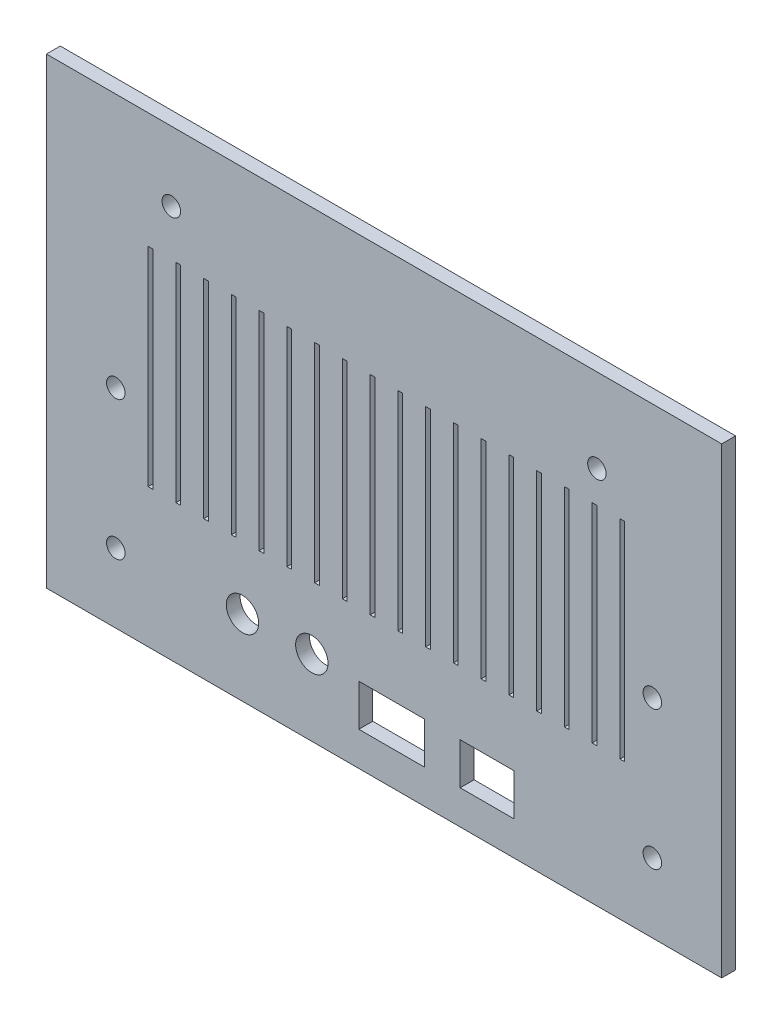
SolidWorks part; units mm, degrees
ref_plane "Front Plane" through (0, 0, 0) normal (0, 0, 1) x (1, 0, 0)
ref_plane "Top Plane" through (0, 0, 0) normal (0, 1, 0) x (1, 0, 0)
ref_plane "Right Plane" through (0, 0, 0) normal (1, 0, 0) x (0, 0, -1)
sketch "Sketch1" plane through (0, 0, 0) normal (0, 0, 1) x (1, 0, 0)
  line L1 (-48.2442, 79.6334) -> (97.7558, 79.6334)
  line L2 (-48.2442, 79.6334) -> (-48.2442, -20.3666)
  line L3 (-48.2442, -20.3666) -> (97.7558, -20.3666)
  line L4 (97.7558, 79.6334) -> (97.7558, -20.3666)
  dimension "D1" = 146
  dimension "D2" = 100
extrude "Boss-Extrude1" add sketch "Sketch1" along normal blind 3
sketch "Sketch2" plane through (0, 0, 3) normal (0, 0, 1) x (1, 0, 0)
  line L0 (-20.2442, 54.6334) -> (-19.2442, 54.6334)
  line L1 (-26.2442, 54.6334) -> (-25.2442, 54.6334)
  line L2 (-26.2442, 54.6334) -> (-26.2442, 9.6334)
  line L3 (-26.2442, 9.6334) -> (-25.2442, 9.6334)
  line L4 (-25.2442, 54.6334) -> (-25.2442, 9.6334)
  line L5 (-20.2442, 54.6334) -> (-20.2442, 9.6334)
  line L6 (-20.2442, 9.6334) -> (-19.2442, 9.6334)
  line L7 (-19.2442, 54.6334) -> (-19.2442, 9.6334)
  line L8 (-14.2442, 54.6334) -> (-13.2442, 54.6334)
  line L9 (-14.2442, 54.6334) -> (-14.2442, 9.6334)
  line L10 (-14.2442, 9.6334) -> (-13.2442, 9.6334)
  line L11 (-13.2442, 54.6334) -> (-13.2442, 9.6334)
  line L12 (-8.2442, 54.6334) -> (-7.2442, 54.6334)
  line L13 (-8.2442, 54.6334) -> (-8.2442, 9.6334)
  line L14 (-8.2442, 9.6334) -> (-7.2442, 9.6334)
  line L15 (-7.2442, 54.6334) -> (-7.2442, 9.6334)
  line L16 (-2.2442, 54.6334) -> (-1.2442, 54.6334)
  line L17 (-2.2442, 54.6334) -> (-2.2442, 9.6334)
  line L18 (-2.2442, 9.6334) -> (-1.2442, 9.6334)
  line L19 (-1.2442, 54.6334) -> (-1.2442, 9.6334)
  line L20 (3.7558, 54.6334) -> (4.7558, 54.6334)
  line L21 (3.7558, 54.6334) -> (3.7558, 9.6334)
  line L22 (3.7558, 9.6334) -> (4.7558, 9.6334)
  line L23 (4.7558, 54.6334) -> (4.7558, 9.6334)
  line L24 (-48.2442, 79.6334) -> (-48.2442, -20.3666) construction
  line L25 (-48.2442, -20.3666) -> (97.7558, -20.3666) construction
  line L26 (9.7558, 54.6334) -> (10.7558, 54.6334)
  line L27 (9.7558, 54.6334) -> (9.7558, 9.6334)
  line L28 (9.7558, 9.6334) -> (10.7558, 9.6334)
  line L29 (10.7558, 54.6334) -> (10.7558, 9.6334)
  line L30 (15.7558, 54.6334) -> (16.7558, 54.6334)
  line L31 (15.7558, 54.6334) -> (15.7558, 9.6334)
  line L32 (15.7558, 9.6334) -> (16.7558, 9.6334)
  line L33 (16.7558, 54.6334) -> (16.7558, 9.6334)
  line L34 (21.7558, 54.6334) -> (22.7558, 54.6334)
  line L35 (21.7558, 54.6334) -> (21.7558, 9.6334)
  line L36 (21.7558, 9.6334) -> (22.7558, 9.6334)
  line L37 (22.7558, 54.6334) -> (22.7558, 9.6334)
  line L38 (33.7558, 54.6334) -> (34.7558, 54.6334)
  line L39 (27.7558, 54.6334) -> (28.7558, 54.6334)
  line L40 (27.7558, 54.6334) -> (27.7558, 9.6334)
  line L41 (27.7558, 9.6334) -> (28.7558, 9.6334)
  line L42 (28.7558, 54.6334) -> (28.7558, 9.6334)
  line L43 (33.7558, 54.6334) -> (33.7558, 9.6334)
  line L44 (33.7558, 9.6334) -> (34.7558, 9.6334)
  line L45 (34.7558, 54.6334) -> (34.7558, 9.6334)
  line L46 (39.7558, 54.6334) -> (40.7558, 54.6334)
  line L47 (39.7558, 54.6334) -> (39.7558, 9.6334)
  line L48 (39.7558, 9.6334) -> (40.7558, 9.6334)
  line L49 (40.7558, 54.6334) -> (40.7558, 9.6334)
  line L50 (45.7558, 54.6334) -> (46.7558, 54.6334)
  line L51 (45.7558, 54.6334) -> (45.7558, 9.6334)
  line L52 (45.7558, 9.6334) -> (46.7558, 9.6334)
  line L53 (46.7558, 54.6334) -> (46.7558, 9.6334)
  line L54 (51.7558, 54.6334) -> (52.7558, 54.6334)
  line L55 (51.7558, 54.6334) -> (51.7558, 9.6334)
  line L56 (51.7558, 9.6334) -> (52.7558, 9.6334)
  line L57 (52.7558, 54.6334) -> (52.7558, 9.6334)
  line L58 (57.7558, 54.6334) -> (58.7558, 54.6334)
  line L59 (57.7558, 54.6334) -> (57.7558, 9.6334)
  line L60 (57.7558, 9.6334) -> (58.7558, 9.6334)
  line L61 (58.7558, 54.6334) -> (58.7558, 9.6334)
  line L62 (63.7558, 54.6334) -> (64.7558, 54.6334)
  line L63 (63.7558, 54.6334) -> (63.7558, 9.6334)
  line L64 (63.7558, 9.6334) -> (64.7558, 9.6334)
  line L65 (64.7558, 54.6334) -> (64.7558, 9.6334)
  line L66 (69.7558, 54.6334) -> (70.7558, 54.6334)
  line L67 (69.7558, 54.6334) -> (69.7558, 9.6334)
  line L68 (69.7558, 9.6334) -> (70.7558, 9.6334)
  line L69 (70.7558, 54.6334) -> (70.7558, 9.6334)
  line L70 (75.7558, 54.6334) -> (76.7558, 54.6334)
  line L71 (75.7558, 54.6334) -> (75.7558, 9.6334)
  line L72 (75.7558, 9.6334) -> (76.7558, 9.6334)
  line L73 (76.7558, 54.6334) -> (76.7558, 9.6334)
  line L74 (97.7558, -20.3666) -> (97.7558, 79.6334) construction
  dimension "D1" = 1
  dimension "D2" = 45
  dimension "D3" = 45
  dimension "D4" = 45
  dimension "D5" = 45
  dimension "D6" = 45
  dimension "D7" = 5
  dimension "D8" = 5
  dimension "D9" = 5
  dimension "D10" = 5
  dimension "D11" = 0
  dimension "D12" = 0
  dimension "D13" = 0
  dimension "D14" = 0
  dimension "D15" = 45
  dimension "D16" = 5
  dimension "D17" = 0
  dimension "D18" = 22
  dimension "D19" = 30
  dimension "D20" = 1
  dimension "D21" = 1
  dimension "D22" = 1
  dimension "D23" = 1
  dimension "D24" = 1
  dimension "D25" = 1
  dimension "D26" = 45
  dimension "D27" = 1
  dimension "D28" = 45
  dimension "D29" = 1
  dimension "D30" = 45
  dimension "D31" = 5
  dimension "D32" = 5
  dimension "D33" = 5
  dimension "D34" = 0
  dimension "D35" = 0
  dimension "D36" = 0
  dimension "D37" = 1
  dimension "D38" = 45
  dimension "D39" = 45
  dimension "D40" = 45
  dimension "D41" = 45
  dimension "D42" = 45
  dimension "D43" = 5
  dimension "D44" = 5
  dimension "D45" = 0
  dimension "D46" = 0
  dimension "D47" = 0
  dimension "D48" = 0
  dimension "D49" = 45
  dimension "D50" = 5
  dimension "D51" = 0
  dimension "D52" = 1
  dimension "D53" = 1
  dimension "D54" = 1
  dimension "D55" = 1
  dimension "D56" = 1
  dimension "D57" = 1
  dimension "D58" = 45
  dimension "D59" = 45
  dimension "D60" = 5
  dimension "D61" = 0
  dimension "D62" = 0
  dimension "D63" = 0
  dimension "D64" = 0
  dimension "D65" = 5
  dimension "D66" = 5
  dimension "D67" = 5
  dimension "D68" = 5
  dimension "D69" = 5
  dimension "D70" = 1
  dimension "D71" = 1
  dimension "D72" = 21
extrude "Cut-Extrude1" cut sketch "Sketch2" against normal through all
sketch "Sketch3" plane through (0, 0, 3) normal (0, 0, 1) x (1, 0, 0)
  circle A0 centre (-33.2442, -5.3666) radius 2
  circle A1 centre (82.7558, -5.3666) radius 2
  dimension "D1" = 4
  dimension "D2" = 4
extrude "Cut-Extrude2" cut sketch "Sketch3" against normal through all
sketch "Sketch4" plane through (0, 0, 0) normal (0, 0, -1) x (-1, 0, 0)
  line L0 (-50.8358, -6.0213) -> (-43.2158, -6.0213) construction
  line L1 (-52.8358, -13.0213) -> (-41.2158, -13.0213)
  line L2 (-52.8358, -13.0213) -> (-52.8358, -4.0213)
  line L3 (-52.8358, -4.0213) -> (-41.2158, -4.0213)
  line L4 (-41.2158, -13.0213) -> (-41.2158, -4.0213)
  line L5 (-50.8358, -11.0213) -> (-43.2158, -11.0213) construction
  line L6 (-50.8358, -11.0213) -> (-50.8358, -6.0213) construction
  line L7 (-43.2158, -11.0213) -> (-43.2158, -6.0213) construction
  dimension "D1" = 2
  dimension "D2" = 2
  dimension "D3" = 2
  dimension "D4" = 2
extrude "Cut-Extrude3" cut sketch "Sketch4" against normal through all
sketch "Sketch5" plane through (0, 0, 3) normal (0, 0, 1) x (1, 0, 0)
  line L0 (21.3058, -6.0213) -> (31.4658, -6.0213) construction
  line L1 (19.3058, -4.0213) -> (33.4658, -4.0213)
  line L2 (19.3058, -4.0213) -> (19.3058, -13.0213)
  line L3 (19.3058, -13.0213) -> (33.4658, -13.0213)
  line L4 (33.4658, -4.0213) -> (33.4658, -13.0213)
  line L5 (21.3058, -6.0213) -> (21.3058, -11.0213) construction
  line L6 (31.4658, -6.0213) -> (31.4658, -11.0213) construction
  line L7 (21.3058, -11.0213) -> (31.4658, -11.0213) construction
  dimension "D1" = 2
  dimension "D2" = 2
  dimension "D3" = 2
  dimension "D4" = 2
extrude "Cut-Extrude4" cut sketch "Sketch5" against normal through all
sketch "Sketch6" plane through (0, 0, 0) normal (0, 0, -1) x (-1, 0, 0)
  line L1 (-33.4658, -4.0213) -> (-19.3058, -4.0213) construction
  circle A0 centre (-9.1392, -4.0213) radius 3.5
  circle A1 centre (5.8608, -4.0213) radius 3.5
  dimension "D2" = 7
  dimension "D1" = 7
  dimension "D3" = 0
  dimension "D4" = 0
  dimension "D5" = 15
extrude "Cut-Extrude5" cut sketch "Sketch6" against normal through all
sketch "Sketch8" plane through (0, 0, 3) normal (0, 0, 1) x (1, 0, 0)
  circle A0 centre (82.7558, 24.6334) radius 2
  circle A1 centre (-33.2442, 24.6334) radius 2
  dimension "D1" = 4
extrude "Cut-Extrude6" cut sketch "Sketch8" against normal through all
sketch "Sketch9" plane through (0, 0, 3) normal (0, 0, 1) x (1, 0, 0)
  circle A0 centre (-21.2442, 64.6334) radius 2
  circle A1 centre (70.7731, 61.5321) radius 2
  dimension "D1" = 4
  dimension "D2" = 4
extrude "Cut-Extrude7" cut sketch "Sketch9" against normal through all
